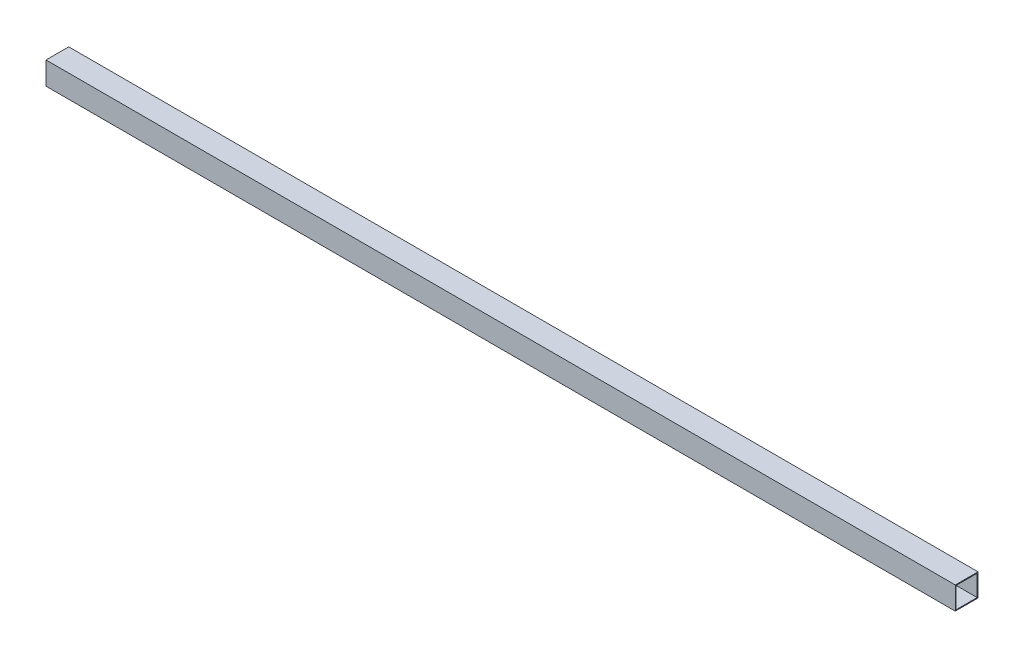
SolidWorks part; units mm, degrees
material "AISI 1020"
ref_plane "Plano frontal" through (0, 0, 0) normal (0, 0, 1) x (1, 0, 0)
ref_plane "Plano superior" through (0, 0, 0) normal (0, 1, 0) x (1, 0, 0)
ref_plane "Plano direito" through (0, 0, 0) normal (1, 0, 0) x (0, 0, -1)
sketch "Esboço1" plane through (0, 0, 0) normal (1, 0, 0) x (0, 0, -1)
  line L1 (-20, -20) -> (20, -20)
  line L2 (-20, -20) -> (-20, 20)
  line L3 (-20, 20) -> (20, 20)
  line L4 (20, -20) -> (20, 20)
  line L5 (-20, -20) -> (20, 20) construction
  line L6 (-20, 20) -> (20, -20) construction
  point P0 (0, 0)
  dimension "D1" = 40
  dimension "D2" = 40
extrude "Ressalto-extrusão1" add sketch "Esboço1" along normal blind 1600
sketch "Esboço2" plane through (0, 0, 0) normal (-1, 0, 0) x (0, 0, 1)
  line L1 (-18.5, -18.5) -> (18.5, -18.5)
  line L2 (-18.5, -18.5) -> (-18.5, 18.5)
  line L3 (-18.5, 18.5) -> (18.5, 18.5)
  line L4 (18.5, -18.5) -> (18.5, 18.5)
  line L5 (-18.5, -18.5) -> (18.5, 18.5) construction
  line L6 (-18.5, 18.5) -> (18.5, -18.5) construction
  point P0 (0, 0)
  dimension "D1" = 37
  dimension "D2" = 37
extrude "Corte-extrusão1" cut sketch "Esboço2" against normal through all
